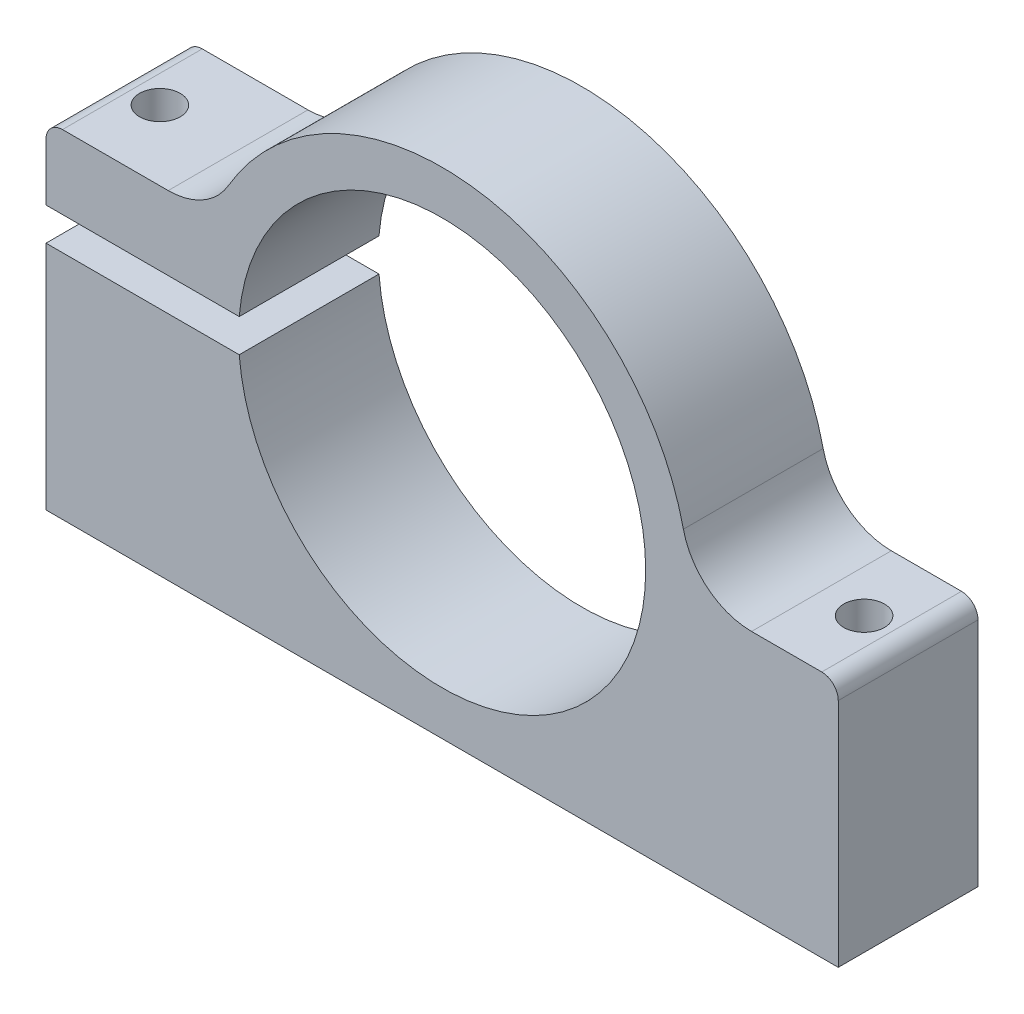
SolidWorks part; units mm, degrees
material "6061 Alloy"
ref_plane "Front Plane" through (0, 0, 0) normal (0, 0, 1) x (1, 0, 0)
ref_plane "Top Plane" through (0, 0, 0) normal (0, 1, 0) x (1, 0, 0)
ref_plane "Right Plane" through (0, 0, 0) normal (1, 0, 0) x (0, 0, -1)
ref_plane "Plane1" through (0, 0, -12.2995) normal (0, 0, -1) x (-1, 0, 0)
sketch "Sketch1" plane through (0, 0, -12.2995) normal (0, 0, -1) x (-1, 0, 0)
  line L0 (24.8593, -22.3859) -> (24.8593, 8.3051)
  line L1 (24.8593, 8.3051) -> (9.7939, 8.3051)
  line L2 (-33.6207, 0.1141) -> (-47.1407, 0.1141)
  line L3 (-47.1407, 0.1141) -> (-47.1407, -22.3859)
  line L4 (-47.1407, -22.3859) -> (24.8593, -22.3859)
  arc A0 (9.7939, 8.3051) -> (-33.6207, 0.1141) centre (-11.1407, 0.1141) ccw
extrude "Boss-Extrude1" add sketch "Sketch1" against normal blind 12.7
sketch "Sketch2" plane through (0, 0, 0.4005) normal (0, 0, 1) x (1, 0, 0)
  line L0 (-24.8593, 1.6141) -> (-24.8593, -1.3859)
  line L1 (-24.8593, -1.3859) -> (-7.2984, -1.3859)
  line L2 (-7.2984, 1.6141) -> (-24.8593, 1.6141)
  arc A0 (-7.2984, -1.3859) -> (-7.2984, 1.6141) centre (11.1407, 0.1141) cw
extrude "Cut-Extrude1" cut sketch "Sketch2" against normal through all
ref_plane "Plane2" through (0, 0.1141, 0) normal (0, -1, 0) x (1, 0, 0)
sketch "Sketch3" plane through (0, 0.1141, 0) normal (0, -1, 0) x (1, 0, 0)
  line L0 (29.6407, 0.4005) -> (11.1407, 0.4005)
  line L1 (11.1407, 0.4005) -> (11.1407, -12.2995)
  line L2 (11.1407, -12.2995) -> (29.6407, -12.2995)
  line L3 (29.6407, -12.2995) -> (29.6407, 0.4005)
  line L4 (11.1407, 0.4005) -> (11.1407, -12.2995) construction
revolve "Cut-Revolve1" cut sketch "Sketch3" angle 360 about L4
hole_wizard "Ø3.7 (3.7) Diameter Hole1" positions "Sketch5" profile "Sketch4" hole size "Ø3.7" standard "ANSI Metric"
sketch "Sketch5" plane through (0, 0.1141, 0) normal (0, 1, 0) x (1, 0, 0)
  point P0 (43.1407, 5.9495)
sketch "Sketch4" plane through (43.1407, 0.1141, -5.9495) normal (1, 0, 0) x (0, 0, 1)
  line L0 (0, 0) -> (0, 22.5)
  line L1 (0, 22.5) -> (1.85, 22.5)
  line L2 (1.85, 22.5) -> (1.85, 0)
  line L5 (1.85, 0) -> (0, 0)
  line L11 (0, -6.35) -> (0, 107.95) construction
  dimension "Thru Hole Dia." = 3.7
  dimension "Thru Hole Depth" = 22.5
hole_wizard "Ø3.7 (3.7) Diameter Hole2" positions "Sketch7" profile "Sketch6" hole size "Ø3.7" standard "ANSI Metric"
sketch "Sketch7" plane through (0, 1.6141, 0) normal (0, -1, 0) x (-1, 0, 0)
  point P0 (20.8593, 5.9495)
sketch "Sketch6" plane through (-20.8593, 1.6141, -5.9495) normal (1, 0, 0) x (0, 0, -1)
  line L0 (0, 0) -> (0, 20.98)
  line L1 (0, 20.98) -> (1.85, 20.98)
  line L2 (1.85, 20.98) -> (1.85, 0)
  line L5 (1.85, 0) -> (0, 0)
  line L11 (0, -6.35) -> (0, 107.95) construction
  dimension "Thru Hole Dia." = 3.7
  dimension "Thru Hole Depth" = 20.98
hole_wizard "Ø3.7 (3.7) Diameter Hole3" positions "Sketch9" profile "Sketch8" hole size "Ø3.7" standard "ANSI Metric"
sketch "Sketch9" plane through (0, -22.3859, 0) normal (0, -1, 0) x (-1, 0, 0)
  point P0 (20.8593, 5.9495)
sketch "Sketch8" plane through (-20.8593, -22.3859, -5.9495) normal (1, 0, 0) x (0, 0, -1)
  line L0 (0, 0) -> (0, 44.98)
  line L1 (0, 44.98) -> (1.85, 44.98)
  line L2 (1.85, 44.98) -> (1.85, 0)
  line L5 (1.85, 0) -> (0, 0)
  line L11 (0, -6.35) -> (0, 107.95) construction
  dimension "Thru Hole Dia." = 3.7
  dimension "Thru Hole Depth" = 44.98
fillet "Fillet1" radius 1.5 2 edges at (-24.8593, 8.3051, -5.9495) (47.1407, 0.1141, -5.9495)
fillet "Fillet2" radius 6.35 2 edges at (33.6207, 0.1141, -5.9495) (-9.7939, 8.3051, -5.9495)
